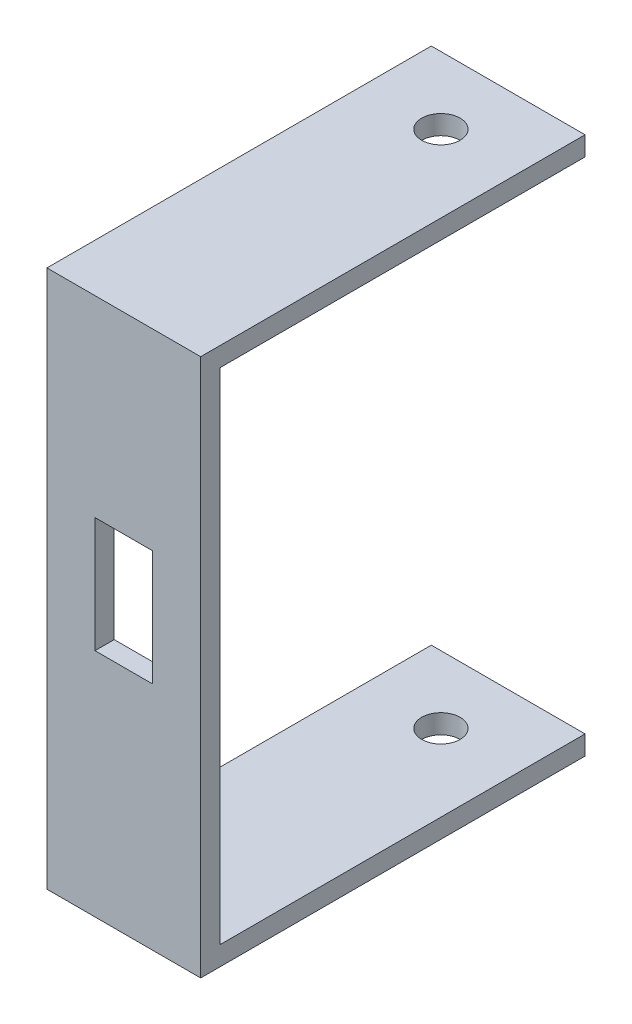
SolidWorks part; units mm, degrees
material "6061-T6 (SS)"
ref_plane "Front Plane" through (0, 0, 0) normal (0, 0, 1) x (1, 0, 0)
ref_plane "Top Plane" through (0, 0, 0) normal (0, 1, 0) x (1, 0, 0)
ref_plane "Right Plane" through (0, 0, 0) normal (1, 0, 0) x (0, 0, -1)
sketch "Sketch1" plane through (0, 0, 0) normal (0, 0, 1) x (1, 0, 0)
  line L1 (-12.7, -41.275) -> (12.7, -41.275)
  line L2 (-12.7, -41.275) -> (-12.7, 41.275)
  line L3 (-12.7, 41.275) -> (12.7, 41.275)
  line L4 (12.7, -41.275) -> (12.7, 41.275)
  line L5 (-12.7, -41.275) -> (12.7, 41.275) construction
  line L6 (-12.7, 41.275) -> (12.7, -41.275) construction
  point P0 (0, 0)
  dimension "D1" = 25.4
  dimension "D2" = 82.55
extrude "Boss-Extrude1" add sketch "Sketch1" along normal blind 3.175
sketch "Sketch2" plane through (0, 41.275, 0) normal (0, 1, 0) x (1, 0, 0)
  line L1 (12.7, -3.175) -> (-12.7, -3.175)
  line L2 (12.7, -3.175) -> (12.7, 60.325)
  line L3 (12.7, 60.325) -> (-12.7, 60.325)
  line L4 (-12.7, -3.175) -> (-12.7, 60.325)
  line L8 (12.7, 0) -> (-12.7, 0)
  line L9 (-12.7, 0) -> (-12.7, -3.175)
  line L10 (-12.7, -3.175) -> (12.7, -3.175)
  line L11 (12.7, -3.175) -> (12.7, 0)
  line L12 (12.7, 0) -> (-12.7, 0)
  line L13 (-12.7, 0) -> (-12.7, -3.175)
  line L14 (-12.7, -3.175) -> (12.7, -3.175)
  line L15 (12.7, -3.175) -> (12.7, 0)
  line M5 (12.7, 0) -> (-12.7, 0)
  line M6 (-12.7, 0) -> (-12.7, -3.175)
  line M7 (-12.7, -3.175) -> (12.7, -3.175)
  line M8 (12.7, -3.175) -> (12.7, 0)
  dimension "D2" = 60.325
  dimension "D1" = 0
extrude "Boss-Extrude2" add sketch "Sketch2" along normal blind 3.175 contours M8 M5 M6 M7 | L4 L2 L3 M5
sketch "Sketch3" plane through (0, -41.275, 0) normal (0, -1, 0) x (1, 0, 0)
  line L1 (12.7, 3.175) -> (-12.7, 3.175)
  line L2 (12.7, 3.175) -> (12.7, -63.5)
  line L3 (12.7, -63.5) -> (-12.7, -63.5)
  line L4 (-12.7, 0) -> (12.7, 0)
  line L5 (12.7, 0) -> (12.7, 3.175)
  line L6 (12.7, 3.175) -> (-12.7, 3.175)
  line L7 (-12.7, 3.175) -> (-12.7, 0)
  line L8 (-12.7, 0) -> (12.7, 0)
  line L9 (12.7, 0) -> (12.7, 3.175)
  line L10 (12.7, 3.175) -> (-12.7, 3.175)
  line L11 (-12.7, 3.175) -> (-12.7, 0)
  line L12 (-12.7, 3.175) -> (-12.7, -63.5)
  dimension "D2" = 63.5
  dimension "D1" = 0
sketch "Sketch5" plane through (0, 0, 3.175) normal (0, 0, 1) x (1, 0, 0)
  line L0 (-12.7, 44.45) -> (12.7, 44.45) construction
  line L1 (-4.7625, 12.7) -> (4.7625, 12.7)
  line L2 (-4.7625, 12.7) -> (-4.7625, -6.35)
  line L3 (-4.7625, -6.35) -> (4.7625, -6.35)
  line L4 (4.7625, 12.7) -> (4.7625, -6.35)
  line L5 (-4.7625, 12.7) -> (4.7625, -6.35) construction
  line L6 (-4.7625, -6.35) -> (4.7625, 12.7) construction
  line L7 (12.7, -44.45) -> (-12.7, -44.45) construction
  point P0 (0, 3.175)
  dimension "D1" = 19.05
  dimension "D2" = 9.525
  dimension "D3" = 41.275
  dimension "D4" = 47.625
  dimension "D5" = 0
extrude "Cut-Extrude2" cut sketch "Sketch5" against normal through all
mirror "Mirror1" about plane through (0, 0, 0) normal (0, 1, 0) of "Boss-Extrude2"
sketch "Sketch6" plane through (0, 44.45, 0) normal (0, 1, 0) x (1, 0, 0)
  line L0 (-12.7, -3.175) -> (-12.7, 0) construction
  line L1 (-12.7, -3.175) -> (-12.7, 0)
  line L2 (12.7, 49.2125) -> (-12.7, 49.2125) construction
  line L4 (12.7, -3.175) -> (12.7, 60.325)
  line L5 (12.7, 60.325) -> (-12.7, 60.325)
  line L6 (-12.7, 60.325) -> (-12.7, -3.175)
  line L7 (-12.7, -3.175) -> (12.7, -3.175)
  line L8 (12.7, -3.175) -> (12.7, 60.325)
  line L9 (12.7, 60.325) -> (-12.7, 60.325)
  line L10 (-12.7, 60.325) -> (-12.7, -3.175)
  line L11 (-12.7, -3.175) -> (12.7, -3.175)
  circle A0 centre (0, 49.2125) radius 3.175
  point P2 (-12.7, -1.5875)
  dimension "D3" = 6.35
  dimension "D2" = 50.8
  dimension "D1" = 0
extrude "Cut-Extrude3" cut sketch "Sketch6" against normal through all contours A0
